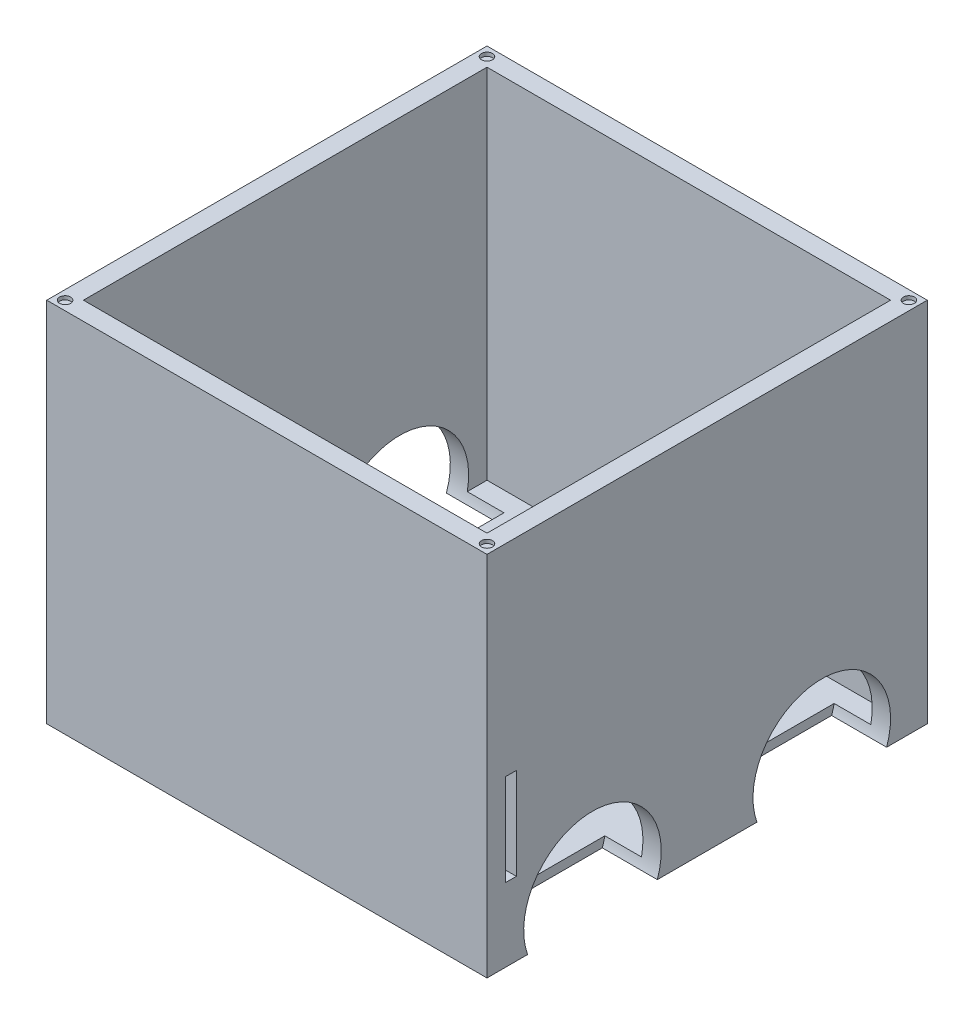
SolidWorks part; units mm, degrees
ref_plane "Front Plane" through (0, 0, 0) normal (0, 0, 1) x (1, 0, 0)
ref_plane "Top Plane" through (0, 0, 0) normal (0, 1, 0) x (1, 0, 0)
ref_plane "Right Plane" through (0, 0, 0) normal (1, 0, 0) x (0, 0, -1)
sketch "Sketch2" plane through (0, -113.102, 0) normal (0, 1, 0) x (1, 0, 0)
  line L1 (-120, -120) -> (120, -120)
  line L2 (-120, -120) -> (-120, 120)
  line L3 (-120, 120) -> (120, 120)
  line L4 (120, -120) -> (120, 120)
  line L5 (-120, -120) -> (120, 120) construction
  line L6 (-120, 120) -> (120, -120) construction
  point P0 (0, 0)
  dimension "D1" = 240
  dimension "D2" = 240
extrude "Boss-Extrude1" add sketch "Sketch2" along normal blind 200
sketch "Sketch17" plane through (0, 86.898, 0) normal (0, 1, 0) x (1, 0, 0)
  line L0 (-110, -110) -> (-110, 110)
  line L1 (-110, 110) -> (110, 110)
  line L2 (110, 110) -> (110, -110)
  line L3 (110, -110) -> (-110, -110)
  line L4 (-120, -120) -> (120, -120) construction
  line L6 (-120, 120) -> (-120, -120) construction
  point P4 (-110, 0)
  dimension "D1" = 220
  dimension "D2" = 10
  dimension "D3" = 220
  dimension "D4" = 10
extrude "Cut-Extrude1" cut sketch "Sketch17" against normal blind 195
sketch "Sketch20" plane through (120, 0, 0) normal (1, 0, 0) x (0, 0, -1)
  line L0 (-120, 86.898) -> (-120, -113.102) construction
  line L1 (120, 86.898) -> (120, -113.102) construction
  line L2 (-120, -113.102) -> (120, -113.102) construction
  circle A0 centre (-62.5, -100.602) radius 37.5
  circle A1 centre (62.5, -100.602) radius 37.5
  point P6 (-100, -100.602)
  point P7 (100, -100.602)
  dimension "D1" = 75
  dimension "D2" = 75
  dimension "D3" = 20
  dimension "D4" = 20
  dimension "D5" = 12.5
  dimension "D6" = 12.5
extrude "Cut-Extrude3" cut sketch "Sketch20" against normal blind 30
sketch "Sketch21" plane through (-120, 0, 0) normal (-1, 0, 0) x (0, 0, 1)
  line L0 (-120, 86.898) -> (-120, -113.102) construction
  line L1 (120, 86.898) -> (120, -113.102) construction
  line L2 (-120, -113.102) -> (120, -113.102) construction
  circle A0 centre (62.5, -100.602) radius 37.5
  circle A1 centre (-62.5, -100.602) radius 37.5
  point P4 (-100, -100.602)
  point P5 (100, -100.602)
  dimension "D5" = 75
  dimension "D6" = 75
  dimension "D1" = 20
  dimension "D2" = 20
  dimension "D3" = 12.5
  dimension "D4" = 12.5
extrude "Cut-Extrude4" cut sketch "Sketch21" against normal blind 30
sketch "Sketch22" plane through (0, 86.898, 0) normal (0, 1, 0) x (1, 0, 0)
  line L0 (-120, 120) -> (-120, -120) construction
  line L1 (120, 120) -> (-120, 120) construction
  line L4 (-110, 0) -> (110, 0) construction
  line L7 (0, -110) -> (0, 110) construction
  circle A0 centre (-115, 115) radius 3
  circle A1 centre (-115, -115) radius 3
  circle A2 centre (115, -115) radius 3
  circle A3 centre (115, 115) radius 3
  dimension "D1" = 6
  dimension "D2" = 5
  dimension "D3" = 5
extrude "Cut-Extrude5" cut sketch "Sketch22" against normal blind 2
sketch "Sketch24" plane through (-120, 0, 0) normal (-1, 0, 0) x (0, 0, 1)
  line L0 (97.8553, -113.102) -> (120, -113.102) construction
  line L2 (110, -73.102) -> (104, -73.102)
  line L3 (104, -73.102) -> (104, -23.102)
  line L4 (104, -23.102) -> (110, -23.102)
  line L5 (110, -23.102) -> (110, -73.102)
  line L8 (120, 86.898) -> (120, -113.102) construction
  point P5 (0, 0)
  point P9 (0, 0)
  dimension "D1" = 40
  dimension "D2" = 50
  dimension "D3" = 6
  dimension "D4" = 10
extrude "Cut-Extrude7" cut sketch "Sketch24" against normal through all both and the other way through all contours L5 L2 L3 L4
